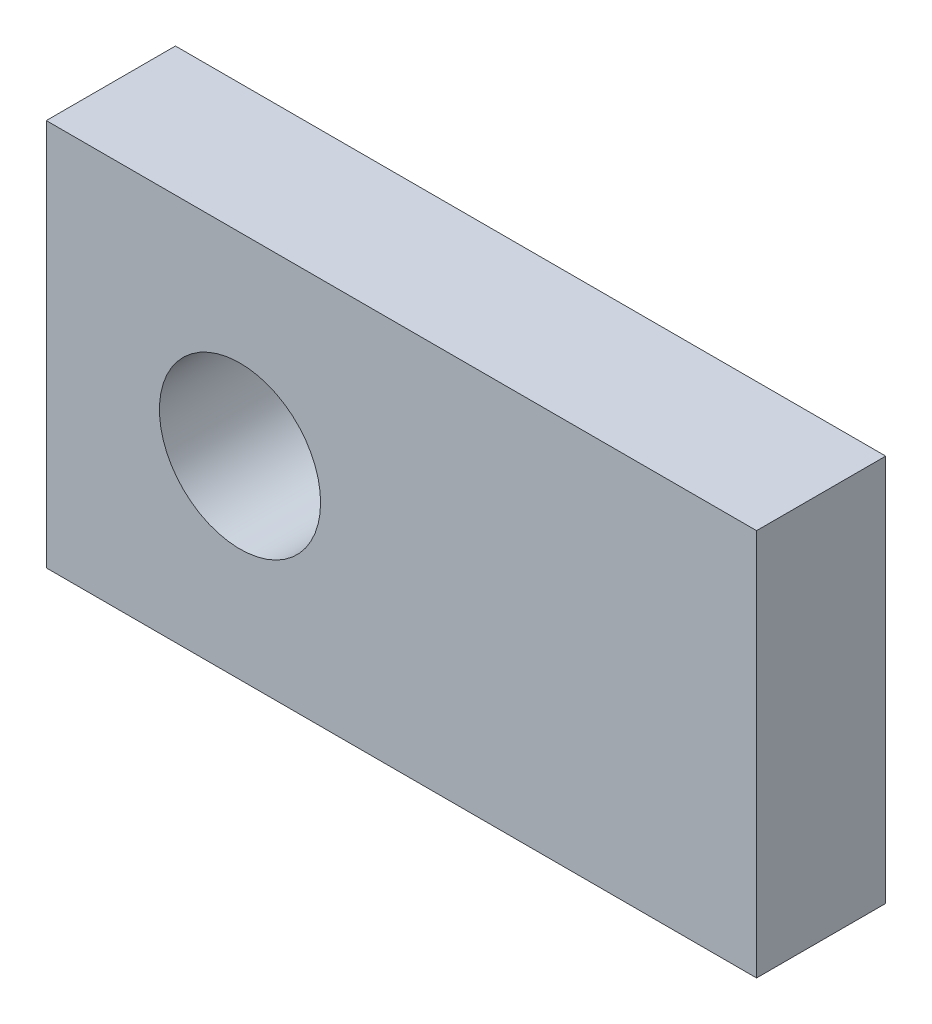
SolidWorks part; units mm, degrees
ref_plane "Front Plane" through (0, 0, 0) normal (0, 0, 1) x (1, 0, 0)
ref_plane "Top Plane" through (0, 0, 0) normal (0, 1, 0) x (1, 0, 0)
ref_plane "Right Plane" through (0, 0, 0) normal (1, 0, 0) x (0, 0, -1)
sketch "Sketch1" plane through (0, 0, 0) normal (0, 0, 1) x (1, 0, 0)
  line L1 (-9.525, 9.525) -> (25.4, 9.525)
  line L2 (-9.525, 9.525) -> (-9.525, -9.525)
  line L3 (-9.525, -9.525) -> (25.4, -9.525)
  line L4 (25.4, 9.525) -> (25.4, -9.525)
  circle A0 centre (0, 0) radius 3.9624
  point P7 (0, 0)
  point P8 (0, 0)
  point P9 (-9.7949, 6.9905)
  dimension "D1" = 7.9248
  dimension "D2" = 9.525
  dimension "D3" = 9.525
  dimension "D4" = 19.05
  dimension "D5" = 34.925
extrude "Boss-Extrude1" add sketch "Sketch1" along normal blind 6.35
